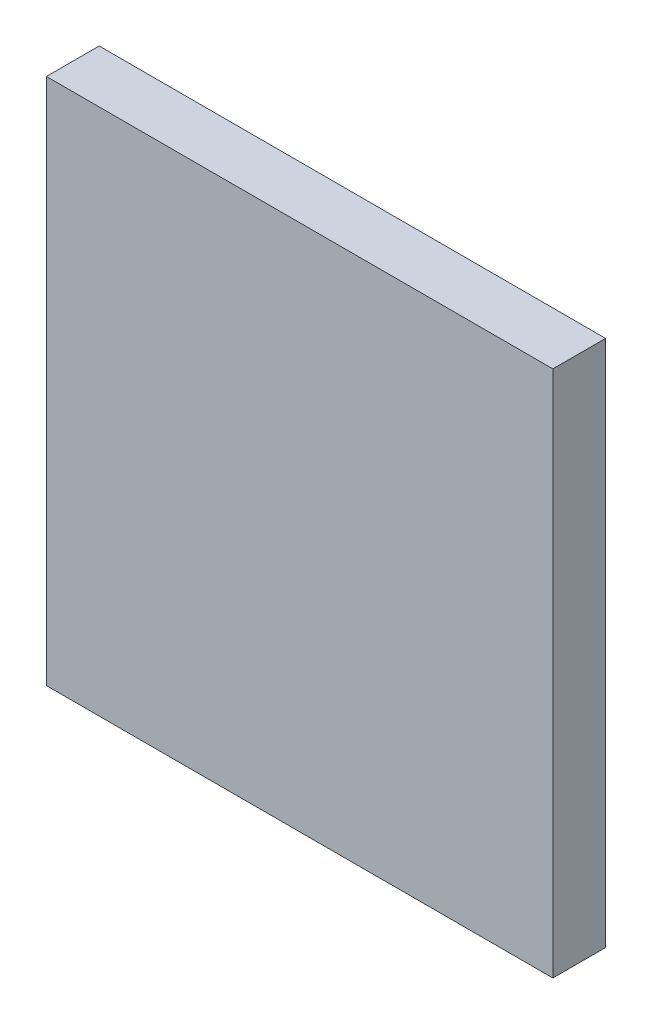
SolidWorks part; units mm, degrees
ref_plane "Front Plane" through (0, 0, 0) normal (0, 0, 1) x (1, 0, 0)
ref_plane "Top Plane" through (0, 0, 0) normal (0, 1, 0) x (1, 0, 0)
ref_plane "Right Plane" through (0, 0, 0) normal (1, 0, 0) x (0, 0, -1)
sketch "Sketch1" plane through (0, 0, 0) normal (0, 0, 1) x (1, 0, 0)
  line L1 (0, 0) -> (240, 0)
  line L2 (0, 0) -> (0, 250)
  line L3 (0, 250) -> (240, 250)
  line L4 (240, 0) -> (240, 250)
  dimension "D1" = 240
  dimension "D2" = 250
extrude "Boss-Extrude1" add sketch "Sketch1" along normal blind 25
